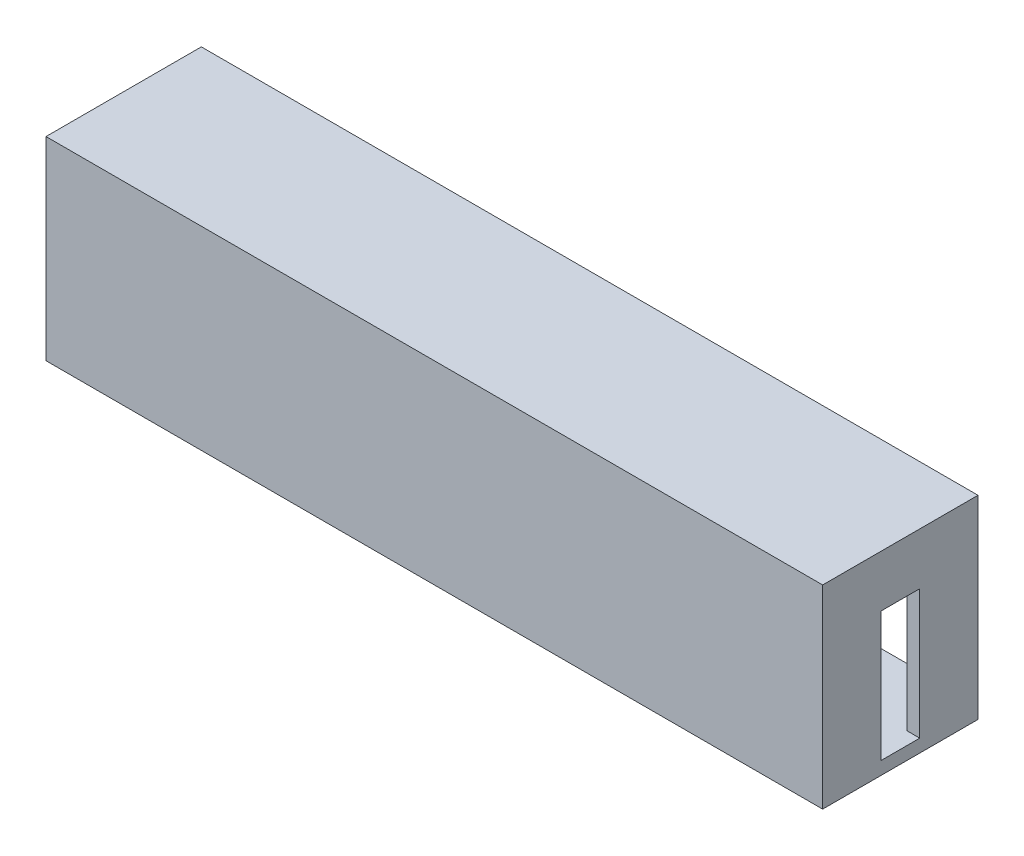
SolidWorks part; units mm, degrees
ref_plane "Front Plane" through (0, 0, 0) normal (0, 0, 1) x (1, 0, 0)
ref_plane "Top Plane" through (0, 0, 0) normal (0, 1, 0) x (1, 0, 0)
ref_plane "Right Plane" through (0, 0, 0) normal (1, 0, 0) x (0, 0, -1)
sketch "Sketch1" plane through (0, 0, 0) normal (0, 0, 1) x (1, 0, 0)
  line L1 (0, 0) -> (12000, 0)
  line L2 (0, 0) -> (0, -3000)
  line L3 (0, -3000) -> (12000, -3000)
  line L4 (12000, 0) -> (12000, -3000)
  line L5 (200, -200) -> (11800, -200)
  line L6 (200, -200) -> (200, -2800)
  line L7 (200, -2800) -> (11800, -2800)
  line L8 (11800, -200) -> (11800, -2800)
  dimension "D1" = 3000
  dimension "D2" = 12000
  dimension "D3" = 200
  dimension "D4" = 200
  dimension "D5" = 200
  dimension "D6" = 200
extrude "Boss-Extrude1" add sketch "Sketch1" along normal blind 2400
sketch "Sketch2" plane through (0, 0, 2400) normal (0, 0, 1) x (1, 0, 0)
  line L4 (0, 0) -> (0, -3000)
  line L5 (0, -3000) -> (12000, -3000)
  line L6 (12000, -3000) -> (12000, 0)
  line L7 (12000, 0) -> (0, 0)
  line L8 (0, 0) -> (0, -3000)
  line L9 (0, -3000) -> (12000, -3000)
  line L10 (12000, -3000) -> (12000, 0)
  line L11 (12000, 0) -> (0, 0)
  dimension "D1" = 0
extrude "Boss-Extrude2" add sketch "Sketch2" against normal blind 200
sketch "Sketch3" plane through (0, 0, 2200) normal (0, 0, -1) x (-1, 0, 0)
  line L0 (-11800, -2800) -> (-11800, -200) construction
  line L1 (-11800, -2120) -> (-200, -2120)
  line L2 (-11800, -2120) -> (-11800, -2180)
  line L3 (-11800, -2180) -> (-200, -2180)
  line L4 (-200, -2120) -> (-200, -2180)
  line L5 (-200, -200) -> (-200, -2800) construction
  line L6 (-200, -2800) -> (-11800, -2800) construction
  dimension "D1" = 60
  dimension "D2" = 680
extrude "Boss-Extrude3" add sketch "Sketch3" along normal blind 700
sketch "Sketch4" plane through (0, 0, 2200) normal (0, 0, -1) x (-1, 0, 0)
  line L0 (-11800, -2800) -> (-11800, -200) construction
  line L1 (-11800, -1600) -> (-200, -1600)
  line L2 (-11800, -1600) -> (-11800, -1640)
  line L3 (-11800, -1640) -> (-200, -1640)
  line L4 (-200, -1600) -> (-200, -1640)
  line L5 (-200, -200) -> (-200, -2120) construction
  line L7 (-200, -2800) -> (-11800, -2800) construction
  line L8 (-11800, -2120) -> (-11800, -200) construction
  line L9 (-11800, -1200) -> (-200, -1200)
  line L10 (-11800, -1200) -> (-11800, -1240)
  line L11 (-11800, -1240) -> (-200, -1240)
  line L12 (-200, -1200) -> (-200, -1240)
  line L13 (-200, -2800) -> (-11800, -2800) construction
  line L14 (-200, -200) -> (-200, -2800) construction
  line L15 (-11800, -800) -> (-200, -800)
  line L16 (-11800, -800) -> (-11800, -840)
  line L17 (-11800, -840) -> (-200, -840)
  line L18 (-200, -800) -> (-200, -840)
  dimension "D1" = 40
  dimension "D2" = 1200
  dimension "D3" = 40
  dimension "D4" = 1600
  dimension "D5" = 40
  dimension "D6" = 2000
extrude "Boss-Extrude4" add sketch "Sketch4" along normal blind 400
sketch "Sketch5" plane through (12000, 0, 0) normal (1, 0, 0) x (0, 0, -1)
  line L0 (-2400, -3000) -> (0, -3000) construction
  line L1 (-1500, -2800) -> (-900, -2800)
  line L2 (-1500, -2800) -> (-1500, -800)
  line L3 (-1500, -800) -> (-900, -800)
  line L4 (-900, -2800) -> (-900, -800)
  line L5 (-2400, -3000) -> (-2400, 0) construction
  dimension "D1" = 200
  dimension "D2" = 600
  dimension "D3" = 2000
  dimension "D4" = 900
extrude "Cut-Extrude1" cut sketch "Sketch5" against normal blind 14169
sketch "Sketch6" plane through (200, 0, 0) normal (1, 0, 0) x (0, 0, -1)
  line L6 (-2400, -3000) -> (-2400, 0) construction
  line L11 (-2400, 0) -> (0, 0) construction
  circle A0 centre (-1200, -400) radius 140
  circle A1 centre (-1200, -400) radius 90
  dimension "D1" = 280
  dimension "D2" = 180
  dimension "D3" = 1200
  dimension "D4" = 400
extrude "Boss-Extrude5" add sketch "Sketch6" along normal blind 11662
